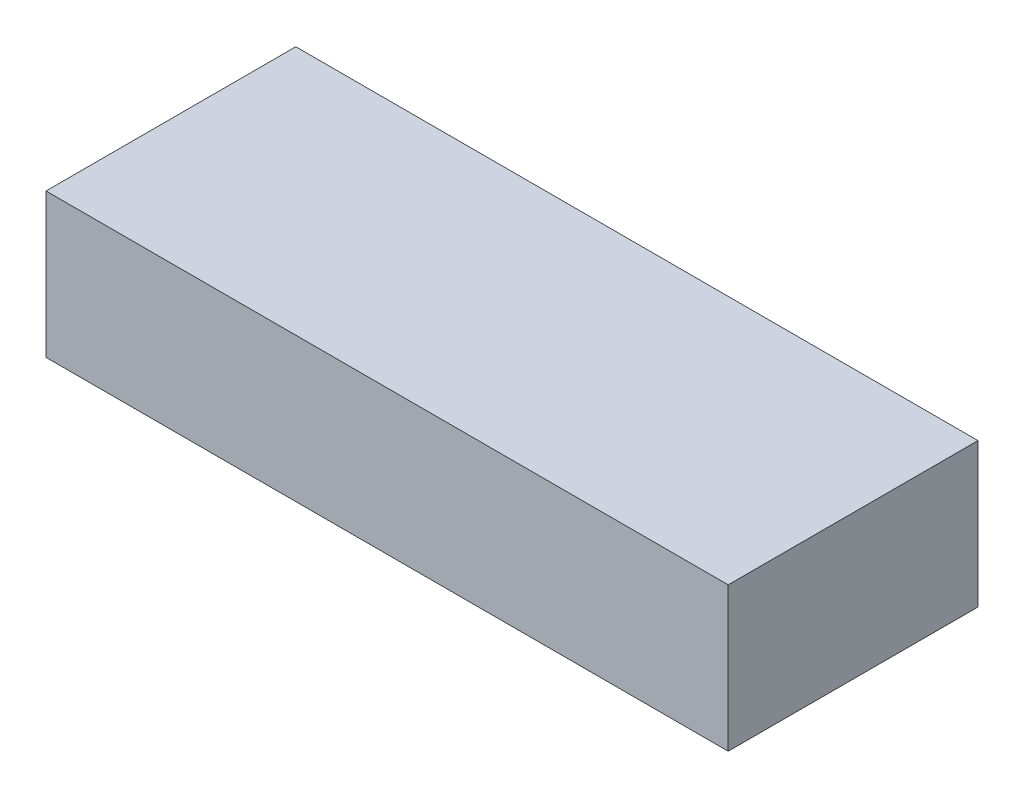
SolidWorks part; units mm, degrees
ref_plane "Ebene vorne" through (0, 0, 0) normal (0, 0, 1) x (1, 0, 0)
ref_plane "Ebene oben" through (0, 0, 0) normal (0, 1, 0) x (1, 0, 0)
ref_plane "Ebene rechts" through (0, 0, 0) normal (1, 0, 0) x (0, 0, -1)
sketch "Sketch1" plane through (0, 0, 0) normal (0, 0, 1) x (1, 0, 0)
  line L1 (-92.7828, -3.765) -> (49.2172, -3.765)
  line L2 (-92.7828, -3.765) -> (-92.7828, -33.765)
  line L3 (-92.7828, -33.765) -> (49.2172, -33.765)
  line L4 (49.2172, -3.765) -> (49.2172, -33.765)
  dimension "D1" = 142
  dimension "D2" = 30
extrude "Boss-Extrude1" add sketch "Sketch1" along normal blind 52
